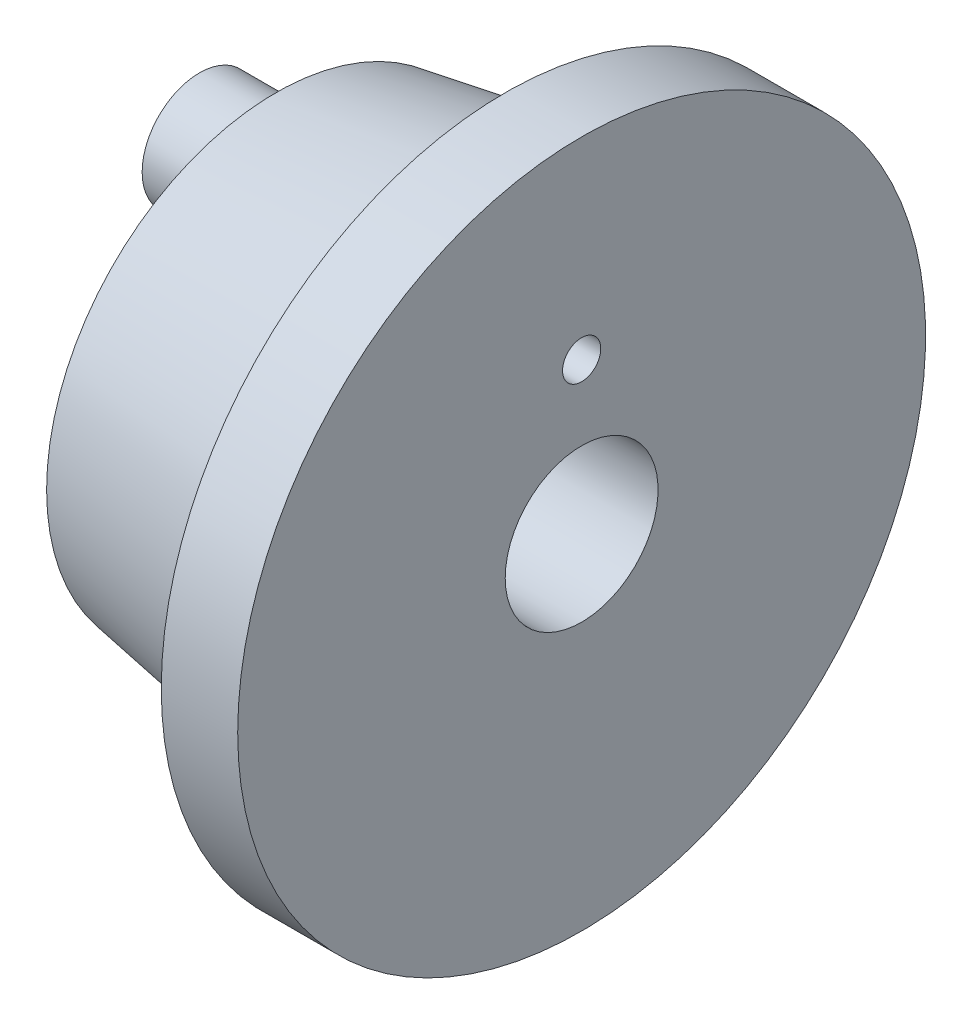
SolidWorks part; units mm, degrees
ref_plane "Front Plane" through (0, 0, 0) normal (0, 0, 1) x (1, 0, 0)
ref_plane "Top Plane" through (0, 0, 0) normal (0, 1, 0) x (1, 0, 0)
ref_plane "Right Plane" through (0, 0, 0) normal (1, 0, 0) x (0, 0, -1)
sketch "Sketch1" plane through (0, 0, 0) normal (0, 0, 1) x (1, 0, 0)
  line L0 (-11.4712, 0) -> (19.7688, 0) construction
  line L1 (0.9275, 4.5) -> (1.9275, 4.5)
  line L2 (1.9275, 4.5) -> (1.9275, 1)
  line L3 (-2.0725, 1) -> (-2.0725, 3)
  line L4 (0.9275, 4.5) -> (0.9275, 3.5)
  line L7 (-2.0725, 1) -> (1.9275, 1)
  line L8 (-2.0725, 3) -> (0.9275, 3.5)
  dimension "D1" = 9
  dimension "D2" = 1
  dimension "D3" = 6
  dimension "D4" = 2
  dimension "D5" = 4
  dimension "D6" = 7
revolve "Revolve1" add sketch "Sketch1" angle 360 about L0
sketch "Sketch3" plane through (-2.0725, 0, 0) normal (-1, 0, 0) x (0, 0, 1)
  circle A0 centre (0, 1.9745) radius 0.25
  dimension "D1" = 0.5
extrude "Cut-Extrude1" cut sketch "Sketch3" against normal up to surface (4 mm away) up to face at (1.9275, 0, 4.5)
sketch "Sketch4" plane through (-2.0725, 0, 0) normal (-1, 0, 0) x (0, 0, 1)
  circle A0 centre (0, 1.9745) radius 0.25 construction
  circle A1 centre (0, 1.9745) radius 0.25
  circle A2 centre (0, 1.9745) radius 0.75
  dimension "D1" = 0.5
extrude "Boss-Extrude1" add sketch "Sketch4" along normal blind 1
sketch "Sketch2" plane through (1.9275, 0, 0) normal (1, 0, 0) x (0, 0, -1)
  circle A0 centre (-0.2076, 2.4914) radius 0.75
  circle A1 centre (-0.2076, 2.4914) radius 1.25
  dimension "D2" = 1.5
  dimension "D1" = 2.5
  dimension "D3" = 0.5
